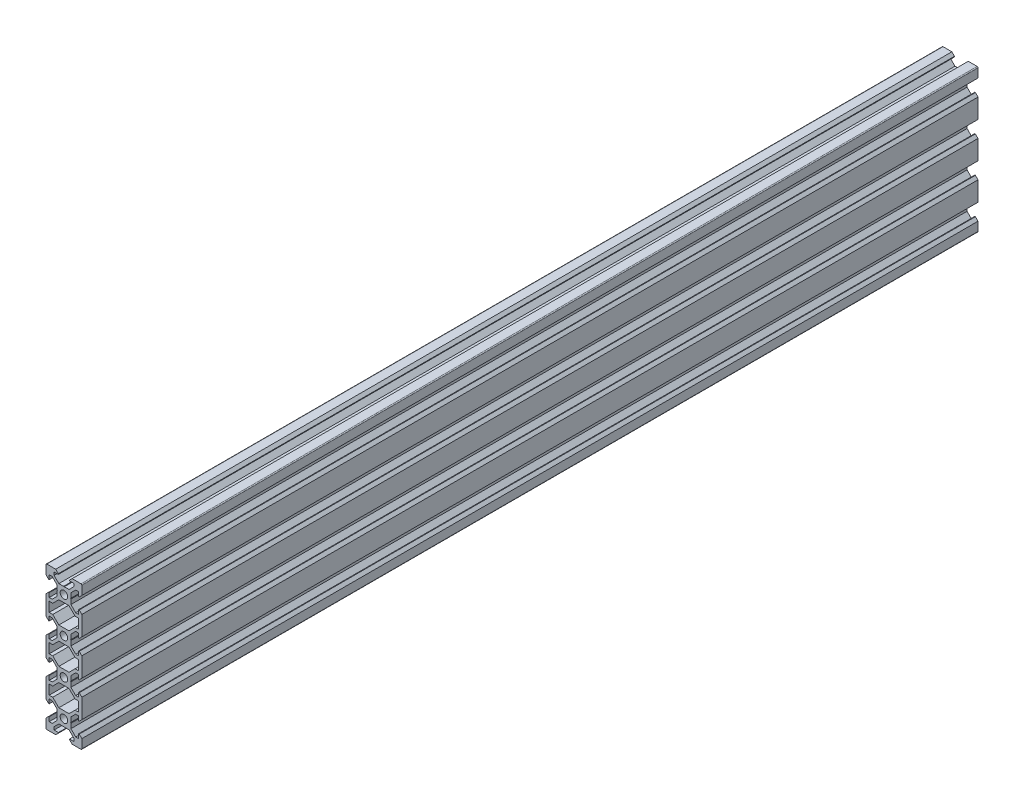
SolidWorks part; units mm, degrees
material "6061-T6 (SS)"
ref_plane "Front Plane" through (0, 0, 0) normal (0, 0, 1) x (1, 0, 0)
ref_plane "Top Plane" through (0, 0, 0) normal (0, 1, 0) x (1, 0, 0)
ref_plane "Right Plane" through (0, 0, 0) normal (1, 0, 0) x (0, 0, -1)
sketch "Sketch1" plane through (0, 0, 0) normal (0, 0, 1) x (1, 0, 0)
  line L0 (0, 0) -> (10, 0) construction
  line L1 (9.5, -40) -> (-9.5, -40)
  line L2 (10, -39.5) -> (10, 39.5)
  line L3 (9.5, 40) -> (-9.5, 40)
  line L4 (-10, -39.5) -> (-10, 39.5)
  line L5 (10, -40) -> (-10, 40) construction
  line L6 (10, 40) -> (-10, -40) construction
  circle A0 centre (0, 30) radius 2.1
  circle A1 centre (0, 10) radius 2.1
  circle A2 centre (0, -10) radius 2.1
  circle A3 centre (0, -30) radius 2.1
  arc A4 (-9.5, -40) -> (-10, -39.5) centre (-9.5, -39.5) cw
  arc A5 (9.5, -40) -> (10, -39.5) centre (9.5, -39.5) ccw
  arc A6 (10, 39.5) -> (9.5, 40) centre (9.5, 39.5) ccw
  arc A7 (-9.5, 40) -> (-10, 39.5) centre (-9.5, 39.5) ccw
  point P0 (0, 0)
  line B0 (0, 30) -> (0, 40) construction
  line B1 (0, 33.69) -> (-0.21, 33.9)
  line B2 (-0.21, 33.9) -> (-2.8393, 33.9)
  line B3 (-2.8393, 33.9) -> (-5.5, 36.5607)
  line B4 (-5.5, 36.5607) -> (-5.5, 38.2)
  line B5 (-5.5, 38.2) -> (-3.125, 38.2)
  line B6 (-3.125, 38.2) -> (-3.125, 38.545)
  line B7 (-3.125, 38.545) -> (-4.58, 40)
  line B8 (-4.58, 40) -> (4.58, 40)
  line B9 (0, 30) -> (-5.9132, 35.9132) construction
  line B10 (3.125, 38.545) -> (4.58, 40)
  line B11 (3.125, 38.2) -> (3.125, 38.545)
  line B12 (5.5, 38.2) -> (3.125, 38.2)
  line B13 (5.5, 36.5607) -> (5.5, 38.2)
  line B14 (2.8393, 33.9) -> (5.5, 36.5607)
  line B15 (0.21, 33.9) -> (2.8393, 33.9)
  line B16 (0, 33.69) -> (0.21, 33.9)
  line B17 (0, 30) -> (-10, 30) construction
  line B18 (-3.69, 30) -> (-3.9, 29.79)
  line B19 (-3.9, 29.79) -> (-3.9, 27.1607)
  line B20 (-3.9, 27.1607) -> (-6.5607, 24.5)
  line B21 (-6.5607, 24.5) -> (-8.2, 24.5)
  line B22 (-8.2, 24.5) -> (-8.2, 26.875)
  line B23 (-8.2, 26.875) -> (-8.545, 26.875)
  line B24 (-8.545, 26.875) -> (-10, 25.42)
  line B25 (-10, 25.42) -> (-10, 34.58)
  line B26 (0, 30) -> (-5.9132, 24.0868) construction
  line B27 (-8.545, 33.125) -> (-10, 34.58)
  line B28 (-8.2, 33.125) -> (-8.545, 33.125)
  line B29 (-8.2, 35.5) -> (-8.2, 33.125)
  line B30 (-6.5607, 35.5) -> (-8.2, 35.5)
  line B31 (-3.9, 32.8393) -> (-6.5607, 35.5)
  line B32 (-3.9, 30.21) -> (-3.9, 32.8393)
  line B33 (-3.69, 30) -> (-3.9, 30.21)
  line B34 (0, 10) -> (-10, 10) construction
  line B35 (-3.69, 10) -> (-3.9, 9.79)
  line B36 (-3.9, 9.79) -> (-3.9, 7.1607)
  line B37 (-3.9, 7.1607) -> (-6.5607, 4.5)
  line B38 (-6.5607, 4.5) -> (-8.2, 4.5)
  line B39 (-8.2, 4.5) -> (-8.2, 6.875)
  line B40 (-8.2, 6.875) -> (-8.545, 6.875)
  line B41 (-8.545, 6.875) -> (-10, 5.42)
  line B42 (-10, 5.42) -> (-10, 14.58)
  line B43 (0, 10) -> (-5.9132, 4.0868) construction
  line B44 (-8.545, 13.125) -> (-10, 14.58)
  line B45 (-8.2, 13.125) -> (-8.545, 13.125)
  line B46 (-8.2, 15.5) -> (-8.2, 13.125)
  line B47 (-6.5607, 15.5) -> (-8.2, 15.5)
  line B48 (-3.9, 12.8393) -> (-6.5607, 15.5)
  line B49 (-3.9, 10.21) -> (-3.9, 12.8393)
  line B50 (-3.69, 10) -> (-3.9, 10.21)
  line B51 (0, -10) -> (-10, -10) construction
  line B52 (-3.69, -10) -> (-3.9, -10.21)
  line B53 (-3.9, -10.21) -> (-3.9, -12.8393)
  line B54 (-3.9, -12.8393) -> (-6.5607, -15.5)
  line B55 (-6.5607, -15.5) -> (-8.2, -15.5)
  line B56 (-8.2, -15.5) -> (-8.2, -13.125)
  line B57 (-8.2, -13.125) -> (-8.545, -13.125)
  line B58 (-8.545, -13.125) -> (-10, -14.58)
  line B59 (-10, -14.58) -> (-10, -5.42)
  line B60 (0, -10) -> (-5.9132, -15.9132) construction
  line B61 (-8.545, -6.875) -> (-10, -5.42)
  line B62 (-8.2, -6.875) -> (-8.545, -6.875)
  line B63 (-8.2, -4.5) -> (-8.2, -6.875)
  line B64 (-6.5607, -4.5) -> (-8.2, -4.5)
  line B65 (-3.9, -7.1607) -> (-6.5607, -4.5)
  line B66 (-3.9, -9.79) -> (-3.9, -7.1607)
  line B67 (-3.69, -10) -> (-3.9, -9.79)
  line B68 (0, -30) -> (-10, -30) construction
  line B69 (-3.69, -30) -> (-3.9, -30.21)
  line B70 (-3.9, -30.21) -> (-3.9, -32.8393)
  line B71 (-3.9, -32.8393) -> (-6.5607, -35.5)
  line B72 (-6.5607, -35.5) -> (-8.2, -35.5)
  line B73 (-8.2, -35.5) -> (-8.2, -33.125)
  line B74 (-8.2, -33.125) -> (-8.545, -33.125)
  line B75 (-8.545, -33.125) -> (-10, -34.58)
  line B76 (-10, -34.58) -> (-10, -25.42)
  line B77 (0, -30) -> (-5.9132, -35.9132) construction
  line B78 (-8.545, -26.875) -> (-10, -25.42)
  line B79 (-8.2, -26.875) -> (-8.545, -26.875)
  line B80 (-8.2, -24.5) -> (-8.2, -26.875)
  line B81 (-6.5607, -24.5) -> (-8.2, -24.5)
  line B82 (-3.9, -27.1607) -> (-6.5607, -24.5)
  line B83 (-3.9, -29.79) -> (-3.9, -27.1607)
  line B84 (-3.69, -30) -> (-3.9, -29.79)
  line B85 (0, -30) -> (0, -40) construction
  line B86 (0, -33.69) -> (0.21, -33.9)
  line B87 (0.21, -33.9) -> (2.8393, -33.9)
  line B88 (2.8393, -33.9) -> (5.5, -36.5607)
  line B89 (5.5, -36.5607) -> (5.5, -38.2)
  line B90 (5.5, -38.2) -> (3.125, -38.2)
  line B91 (3.125, -38.2) -> (3.125, -38.545)
  line B92 (3.125, -38.545) -> (4.58, -40)
  line B93 (4.58, -40) -> (-4.58, -40)
  line B94 (0, -30) -> (5.9132, -35.9132) construction
  line B95 (-3.125, -38.545) -> (-4.58, -40)
  line B96 (-3.125, -38.2) -> (-3.125, -38.545)
  line B97 (-5.5, -38.2) -> (-3.125, -38.2)
  line B98 (-5.5, -36.5607) -> (-5.5, -38.2)
  line B99 (-2.8393, -33.9) -> (-5.5, -36.5607)
  line B100 (-0.21, -33.9) -> (-2.8393, -33.9)
  line B101 (0, -33.69) -> (-0.21, -33.9)
  line B102 (0, -30) -> (10, -30) construction
  line B103 (3.69, -30) -> (3.9, -29.79)
  line B104 (3.9, -29.79) -> (3.9, -27.1607)
  line B105 (3.9, -27.1607) -> (6.5607, -24.5)
  line B106 (6.5607, -24.5) -> (8.2, -24.5)
  line B107 (8.2, -24.5) -> (8.2, -26.875)
  line B108 (8.2, -26.875) -> (8.545, -26.875)
  line B109 (8.545, -26.875) -> (10, -25.42)
  line B110 (10, -25.42) -> (10, -34.58)
  line B111 (0, -30) -> (5.9132, -24.0868) construction
  line B112 (8.545, -33.125) -> (10, -34.58)
  line B113 (8.2, -33.125) -> (8.545, -33.125)
  line B114 (8.2, -35.5) -> (8.2, -33.125)
  line B115 (6.5607, -35.5) -> (8.2, -35.5)
  line B116 (3.9, -32.8393) -> (6.5607, -35.5)
  line B117 (3.9, -30.21) -> (3.9, -32.8393)
  line B118 (3.69, -30) -> (3.9, -30.21)
  line B119 (0, -10) -> (10, -10) construction
  line B120 (3.69, -10) -> (3.9, -9.79)
  line B121 (3.9, -9.79) -> (3.9, -7.1607)
  line B122 (3.9, -7.1607) -> (6.5607, -4.5)
  line B123 (6.5607, -4.5) -> (8.2, -4.5)
  line B124 (8.2, -4.5) -> (8.2, -6.875)
  line B125 (8.2, -6.875) -> (8.545, -6.875)
  line B126 (8.545, -6.875) -> (10, -5.42)
  line B127 (10, -5.42) -> (10, -14.58)
  line B128 (0, -10) -> (5.9132, -4.0868) construction
  line B129 (8.545, -13.125) -> (10, -14.58)
  line B130 (8.2, -13.125) -> (8.545, -13.125)
  line B131 (8.2, -15.5) -> (8.2, -13.125)
  line B132 (6.5607, -15.5) -> (8.2, -15.5)
  line B133 (3.9, -12.8393) -> (6.5607, -15.5)
  line B134 (3.9, -10.21) -> (3.9, -12.8393)
  line B135 (3.69, -10) -> (3.9, -10.21)
  line B136 (0, 10) -> (10, 10) construction
  line B137 (3.69, 10) -> (3.9, 10.21)
  line B138 (3.9, 10.21) -> (3.9, 12.8393)
  line B139 (3.9, 12.8393) -> (6.5607, 15.5)
  line B140 (6.5607, 15.5) -> (8.2, 15.5)
  line B141 (8.2, 15.5) -> (8.2, 13.125)
  line B142 (8.2, 13.125) -> (8.545, 13.125)
  line B143 (8.545, 13.125) -> (10, 14.58)
  line B144 (10, 14.58) -> (10, 5.42)
  line B145 (0, 10) -> (5.9132, 15.9132) construction
  line B146 (8.545, 6.875) -> (10, 5.42)
  line B147 (8.2, 6.875) -> (8.545, 6.875)
  line B148 (8.2, 4.5) -> (8.2, 6.875)
  line B149 (6.5607, 4.5) -> (8.2, 4.5)
  line B150 (3.9, 7.1607) -> (6.5607, 4.5)
  line B151 (3.9, 9.79) -> (3.9, 7.1607)
  line B152 (3.69, 10) -> (3.9, 9.79)
  line B153 (0, 30) -> (10, 30) construction
  line B154 (3.69, 30) -> (3.9, 30.21)
  line B155 (3.9, 30.21) -> (3.9, 32.8393)
  line B156 (3.9, 32.8393) -> (6.5607, 35.5)
  line B157 (6.5607, 35.5) -> (8.2, 35.5)
  line B158 (8.2, 35.5) -> (8.2, 33.125)
  line B159 (8.2, 33.125) -> (8.545, 33.125)
  line B160 (8.545, 33.125) -> (10, 34.58)
  line B161 (10, 34.58) -> (10, 25.42)
  line B162 (0, 30) -> (5.9132, 35.9132) construction
  line B163 (8.545, 26.875) -> (10, 25.42)
  line B164 (8.2, 26.875) -> (8.545, 26.875)
  line B165 (8.2, 24.5) -> (8.2, 26.875)
  line B166 (6.5607, 24.5) -> (8.2, 24.5)
  line B167 (3.9, 27.1607) -> (6.5607, 24.5)
  line B168 (3.9, 29.79) -> (3.9, 27.1607)
  line B169 (3.69, 30) -> (3.9, 29.79)
  line B170 (-8.2, 17.3) -> (-8.2, 22.7)
  line B171 (-8.2, 22.7) -> (-6.2393, 22.7)
  line B172 (-6.2393, 22.7) -> (-2.8393, 26.1)
  line B173 (-2.8393, 26.1) -> (2.8393, 26.1)
  line B174 (0, 26.1) -> (0, 20) construction
  line B175 (0, 20) -> (-8.2, 20) construction
  line B176 (6.2393, 22.7) -> (2.8393, 26.1)
  line B177 (8.2, 22.7) -> (6.2393, 22.7)
  line B178 (8.2, 17.3) -> (8.2, 22.7)
  line B179 (8.2, 17.3) -> (6.2393, 17.3)
  line B180 (6.2393, 17.3) -> (2.8393, 13.9)
  line B181 (-2.8393, 13.9) -> (2.8393, 13.9)
  line B182 (-6.2393, 17.3) -> (-2.8393, 13.9)
  line B183 (-8.2, 17.3) -> (-6.2393, 17.3)
  line B184 (0, 26.1) -> (0, 30) construction
  line B185 (0, 30) -> (-5.0927, 24.9073) construction
  line B186 (-8.2, -2.7) -> (-8.2, 2.7)
  line B187 (-8.2, 2.7) -> (-6.2393, 2.7)
  line B188 (-6.2393, 2.7) -> (-2.8393, 6.1)
  line B189 (-2.8393, 6.1) -> (2.8393, 6.1)
  line B190 (0, 6.1) -> (0, 0) construction
  line B191 (0, 0) -> (-8.2, 0) construction
  line B192 (6.2393, 2.7) -> (2.8393, 6.1)
  line B193 (8.2, 2.7) -> (6.2393, 2.7)
  line B194 (8.2, -2.7) -> (8.2, 2.7)
  line B195 (8.2, -2.7) -> (6.2393, -2.7)
  line B196 (6.2393, -2.7) -> (2.8393, -6.1)
  line B197 (-2.8393, -6.1) -> (2.8393, -6.1)
  line B198 (-6.2393, -2.7) -> (-2.8393, -6.1)
  line B199 (-8.2, -2.7) -> (-6.2393, -2.7)
  line B200 (0, 6.1) -> (0, 10) construction
  line B201 (0, 10) -> (-5.0927, 4.9073) construction
  line B202 (-8.2, -22.7) -> (-8.2, -17.3)
  line B203 (-8.2, -17.3) -> (-6.2393, -17.3)
  line B204 (-6.2393, -17.3) -> (-2.8393, -13.9)
  line B205 (-2.8393, -13.9) -> (2.8393, -13.9)
  line B206 (0, -13.9) -> (0, -20) construction
  line B207 (0, -20) -> (-8.2, -20) construction
  line B208 (6.2393, -17.3) -> (2.8393, -13.9)
  line B209 (8.2, -17.3) -> (6.2393, -17.3)
  line B210 (8.2, -22.7) -> (8.2, -17.3)
  line B211 (8.2, -22.7) -> (6.2393, -22.7)
  line B212 (6.2393, -22.7) -> (2.8393, -26.1)
  line B213 (-2.8393, -26.1) -> (2.8393, -26.1)
  line B214 (-6.2393, -22.7) -> (-2.8393, -26.1)
  line B215 (-8.2, -22.7) -> (-6.2393, -22.7)
  line B216 (0, -13.9) -> (0, -10) construction
  line B217 (0, -10) -> (-5.0927, -15.0927) construction
  dimension "D5" = 4.2
  dimension "D6" = 0.5
  dimension "D1" = 20
  dimension "D2" = 80
  dimension "D3" = 20
  dimension "D4" = 20
sketch_block_instance "V Slot 1-4"
sketch_block "V Slot 1" parameters "D1"=10, "D2"=11, "D3"=4.3, "D4"=1.8, "D5"=0.21, "D6"=45, "D7"=9.16, "D8"=1.5, "D9"=6.25
sketch_block_instance "V Slot 1-5"
sketch_block_instance "V Slot 1-6"
sketch_block_instance "V Slot 1-7"
sketch_block_instance "V Slot 1-8"
sketch_block_instance "V Slot 1-9"
sketch_block_instance "V Slot 1-10"
sketch_block_instance "V Slot 1-11"
sketch_block_instance "V Slot 1-12"
sketch_block_instance "V Slot 1-13"
sketch_block_instance "Center Cutout 1-1"
sketch_block "Center Cutout 1" parameters "D1"=5.4, "D2"=12.2, "D3"=8.2, "D4"=45, "D5"=10, "D6"=1.5
sketch_block_instance "Center Cutout 1-2"
sketch_block_instance "Center Cutout 1-3"
extrude "Boss-Extrude1" add sketch "Sketch1" along normal blind 500 contours B169 B154 B155 B156 B157 B158 B159 B160 L2 A6 L3 B10 B11 B12 B13 B14 B15 B16 B1 B2 B3 B4 B5 B6 B7 A7 L4 B27 B28 B29 B30 B31 B32 B33 B18 B19 B20 B21 B22 B23 B24 B44 B45 B46 B47 B48 B49 B50 B35
